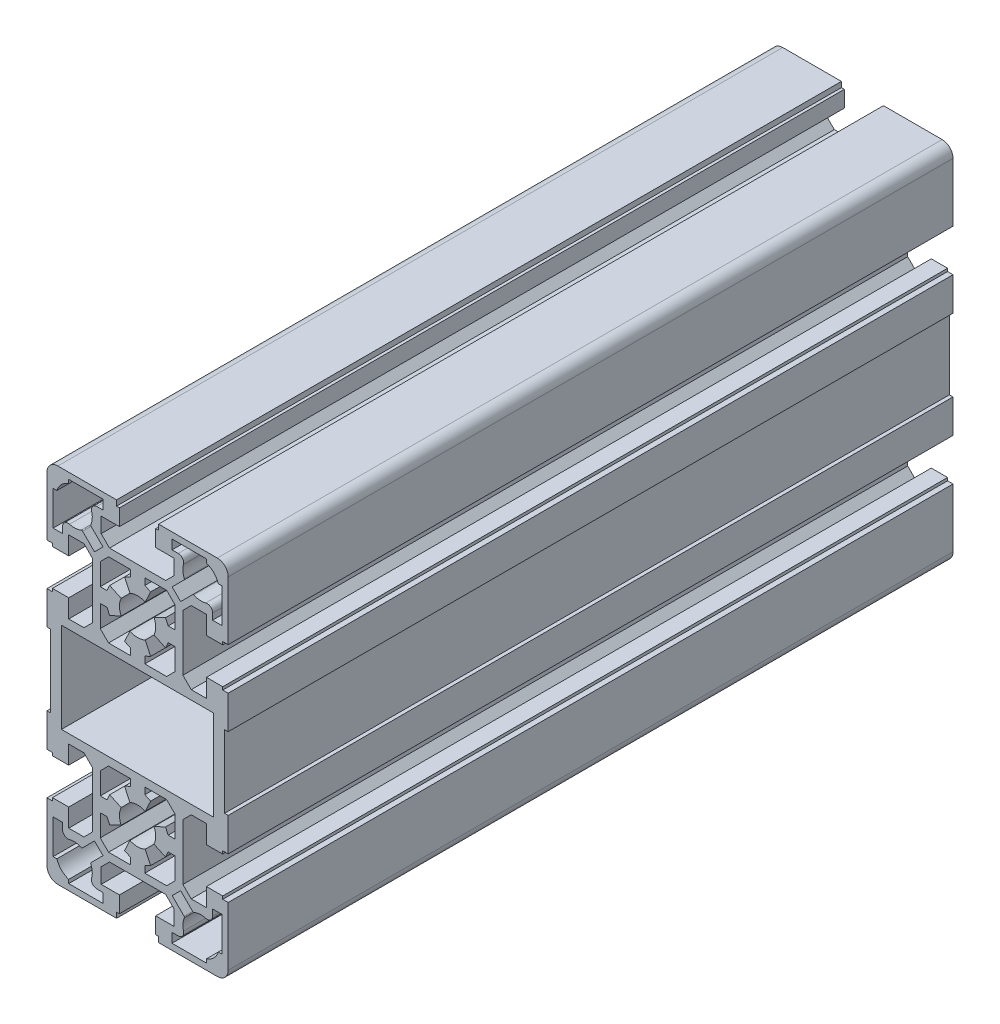
SolidWorks part; units mm, degrees
ref_plane "Front Plane" through (0, 0, 0) normal (0, 0, 1) x (1, 0, 0)
ref_plane "Top Plane" through (0, 0, 0) normal (0, 1, 0) x (1, 0, 0)
ref_plane "Right Plane" through (0, 0, 0) normal (1, 0, 0) x (0, 0, -1)
sketch "Sketch1" plane through (0, 0, 0) normal (0, 0, 1) x (1, 0, 0)
  line L0 (9.5389, 61.8847) -> (12.8447, 65.1906)
  line L1 (25, 72) -> (25, 55.8)
  line L2 (23.3, 69) -> (23.3, 59.5)
  line L3 (-10.05, 64.8) -> (-7.75, 62.5)
  line L4 (-12.8447, 65.1906) -> (-9.5389, 61.8847)
  line L5 (-25, 55.8) -> (-25, 72)
  line L6 (-23.3, 59.5) -> (-23.3, 69)
  line L7 (7.75, 62.5) -> (10.05, 64.8)
  line L8 (2, 60.3) -> (8.0123, 60.3)
  line L9 (-7.75, 62.5) -> (7.75, 62.5)
  line L10 (4.5315, 47.8869) -> (7.7036, 46.4077)
  line L11 (8.0123, 39.7) -> (2, 39.7)
  line L12 (7.7036, 53.5923) -> (4.5315, 52.1131)
  line L13 (8.0123, -10.3) -> (2, -10.3)
  line L14 (2, 10.3) -> (8.0123, 10.3)
  line L15 (7.7036, 3.5923) -> (4.5315, 2.1131)
  line L16 (4.5315, -2.1131) -> (7.7036, -3.5923)
  line L17 (7.75, -12.5) -> (-7.75, -12.5)
  line L18 (5, -19) -> (10.05, -19)
  line L19 (22, -25) -> (5.8, -25)
  line L20 (-21, 37.45) -> (21, 37.45)
  line L21 (21, 12.55) -> (-21, 12.55)
  line L22 (-24, 15) -> (-24, 35)
  line L23 (-21, 12.55) -> (-21, 37.45)
  line L24 (3.5923, -7.7036) -> (2.1131, -4.5315)
  line L25 (-2.1131, -4.5315) -> (-3.5923, -7.7036)
  line L26 (-10.3, -8.0123) -> (-10.3, -2)
  line L27 (-12.5, -7.75) -> (-12.5, 7.75)
  line L28 (-19, -5) -> (-19, -10.05)
  line L29 (-25, -22) -> (-25, -5.8)
  line L30 (-10.05, -14.8) -> (-10.05, -19)
  line L31 (-23.3, -19) -> (-23.3, -9.5)
  line L32 (-5.8, -25) -> (-22, -25)
  line L33 (-9.5, -23.3) -> (-19, -23.3)
  line L34 (-22.2697, -19) -> (-23.3, -19)
  line L35 (-19, -23.3) -> (-19, -22.2697)
  line L36 (5.8, -25) -> (5.8, -23.5)
  line L37 (-5.8, -23.5) -> (-5.8, -25)
  line L38 (-10.05, -19) -> (-5, -19)
  line L39 (-11.2262, -20.7) -> (-9.5, -20.7)
  line L40 (-5, -23.5) -> (-5.8, -23.5)
  line L41 (-5, -19) -> (-5, -23.5)
  line L42 (-9.5, -20.7) -> (-9.5, -23.3)
  line L43 (5.8, -23.5) -> (5, -23.5)
  line L44 (5, -23.5) -> (5, -19)
  line L45 (-14.8, -10.05) -> (-12.5, -7.75)
  line L46 (-15.1906, -12.8447) -> (-11.8847, -9.5389)
  line L47 (-19, -10.05) -> (-14.8, -10.05)
  line L48 (-20.7, -9.5) -> (-20.7, -11.2262)
  line L49 (-23.3, -9.5) -> (-20.7, -9.5)
  line L50 (-9.5389, -11.8847) -> (-12.8447, -15.1906)
  line L51 (-7.75, -12.5) -> (-10.05, -14.8)
  line L52 (-3.5923, -7.7036) -> (-2, -8.4461)
  line L53 (-2, -10.3) -> (-8.0123, -10.3)
  line L54 (-11.8847, -9.5389) -> (-9.5389, -11.8847)
  line L55 (-8.0123, -10.3) -> (-10.3, -8.0123)
  line L56 (2, -10.3) -> (2, -8.4461)
  line L57 (2, -8.4461) -> (3.5923, -7.7036)
  line L58 (-2, -8.4461) -> (-2, -10.3)
  line L59 (2.1131, 4.5315) -> (3.5923, 7.7036)
  line L60 (-10.3, 2) -> (-10.3, 8.0123)
  line L61 (-3.5923, 7.7036) -> (-2.1131, 4.5315)
  line L62 (-19, 10.05) -> (-19, 5)
  line L63 (-23.5, 5) -> (-23.5, 5.8)
  line L64 (-25, -5.8) -> (-23.5, -5.8)
  line L65 (-23.5, -5.8) -> (-23.5, -5)
  line L66 (-23.5, -5) -> (-19, -5)
  line L67 (-19, 5) -> (-23.5, 5)
  line L68 (-10.3, -2) -> (-8.4461, -2)
  line L69 (-8.4461, -2) -> (-7.7036, -3.5923)
  line L70 (-7.7036, -3.5923) -> (-4.5315, -2.1131)
  line L71 (-4.5315, 2.1131) -> (-7.7036, 3.5923)
  line L72 (-7.7036, 3.5923) -> (-8.4461, 2)
  line L73 (-8.4461, 2) -> (-10.3, 2)
  line L74 (-12.5, 7.75) -> (-14.8, 10.05)
  line L75 (-25, 5.8) -> (-25, 15)
  line L76 (-23.5, 5.8) -> (-25, 5.8)
  line L77 (-14.8, 10.05) -> (-19, 10.05)
  line L78 (-25, 15) -> (-24, 15)
  line L79 (-8.0123, 10.3) -> (-2, 10.3)
  line L80 (-2, 8.4461) -> (-3.5923, 7.7036)
  line L81 (-10.3, 8.0123) -> (-8.0123, 10.3)
  line L82 (3.5923, 7.7036) -> (2, 8.4461)
  line L83 (2, 8.4461) -> (2, 10.3)
  line L84 (-2, 10.3) -> (-2, 8.4461)
  line L85 (2, 39.7) -> (2, 41.5539)
  line L86 (-2, 41.5539) -> (-2, 39.7)
  line L87 (-8.0123, 39.7) -> (-10.3, 41.9877)
  line L88 (-25, 35) -> (-25, 44.2)
  line L89 (-24, 35) -> (-25, 35)
  line L90 (-2, 39.7) -> (-8.0123, 39.7)
  line L91 (-12.5, 42.25) -> (-12.5, 57.75)
  line L92 (-14.8, 39.95) -> (-12.5, 42.25)
  line L93 (-25, 44.2) -> (-23.5, 44.2)
  line L94 (-19, 39.95) -> (-14.8, 39.95)
  line L95 (-19, 45) -> (-19, 39.95)
  line L96 (-23.5, 44.2) -> (-23.5, 45)
  line L97 (-23.5, 45) -> (-19, 45)
  line L98 (-10.3, 41.9877) -> (-10.3, 48)
  line L99 (-2.1131, 45.4685) -> (-3.5923, 42.2964)
  line L100 (-3.5923, 42.2964) -> (-2, 41.5539)
  line L101 (2, 41.5539) -> (3.5923, 42.2964)
  line L102 (3.5923, 42.2964) -> (2.1131, 45.4685)
  line L103 (-10.3, 48) -> (-8.4461, 48)
  line L104 (-8.4461, 48) -> (-7.7036, 46.4077)
  line L105 (-7.7036, 46.4077) -> (-4.5315, 47.8869)
  line L106 (-12.5, 57.75) -> (-14.8, 60.05)
  line L107 (-11.8847, 59.5389) -> (-15.1906, 62.8447)
  line L108 (-19, 60.05) -> (-19, 55)
  line L109 (-23.5, 55.8) -> (-25, 55.8)
  line L110 (-23.5, 55) -> (-23.5, 55.8)
  line L111 (-19, 55) -> (-23.5, 55)
  line L112 (-14.8, 60.05) -> (-19, 60.05)
  line L113 (-20.7, 59.5) -> (-23.3, 59.5)
  line L114 (-20.7, 61.2262) -> (-20.7, 59.5)
  line L115 (2.1131, 54.5315) -> (3.5923, 57.7036)
  line L116 (-10.3, 52) -> (-10.3, 58.0123)
  line L117 (-3.5923, 57.7036) -> (-2.1131, 54.5315)
  line L118 (-4.5315, 52.1131) -> (-7.7036, 53.5923)
  line L119 (-7.7036, 53.5923) -> (-8.4461, 52)
  line L120 (-8.4461, 52) -> (-10.3, 52)
  line L121 (-8.0123, 60.3) -> (-2, 60.3)
  line L122 (-2, 58.4461) -> (-3.5923, 57.7036)
  line L123 (-10.3, 58.0123) -> (-8.0123, 60.3)
  line L124 (-9.5389, 61.8847) -> (-11.8847, 59.5389)
  line L125 (3.5923, 57.7036) -> (2, 58.4461)
  line L126 (-2, 60.3) -> (-2, 58.4461)
  line L127 (2, 58.4461) -> (2, 60.3)
  line L128 (24, 35) -> (24, 15)
  line L129 (21, 37.45) -> (21, 12.55)
  line L130 (19, -10.05) -> (19, -5)
  line L131 (12.5, 7.75) -> (12.5, -7.75)
  line L132 (10.3, -2) -> (10.3, -8.0123)
  line L133 (25, -5.8) -> (25, -22)
  line L134 (23.3, -9.5) -> (23.3, -19)
  line L135 (10.05, -19) -> (10.05, -14.8)
  line L136 (19, -23.3) -> (9.5, -23.3)
  line L137 (9.5, -20.7) -> (11.2262, -20.7)
  line L138 (9.5, -23.3) -> (9.5, -20.7)
  line L139 (23.3, -19) -> (22.2697, -19)
  line L140 (19, -22.2697) -> (19, -23.3)
  line L141 (12.8447, -15.1906) -> (9.5389, -11.8847)
  line L142 (11.8847, -9.5389) -> (15.1906, -12.8447)
  line L143 (10.05, -14.8) -> (7.75, -12.5)
  line L144 (14.8, -10.05) -> (19, -10.05)
  line L145 (12.5, -7.75) -> (14.8, -10.05)
  line L146 (9.5389, -11.8847) -> (11.8847, -9.5389)
  line L147 (10.3, -8.0123) -> (8.0123, -10.3)
  line L148 (20.7, -11.2262) -> (20.7, -9.5)
  line L149 (20.7, -9.5) -> (23.3, -9.5)
  line L150 (23.5, 5.8) -> (23.5, 5)
  line L151 (19, 5) -> (19, 10.05)
  line L152 (10.3, 8.0123) -> (10.3, 2)
  line L153 (7.7036, -3.5923) -> (8.4461, -2)
  line L154 (8.4461, -2) -> (10.3, -2)
  line L155 (23.5, -5.8) -> (25, -5.8)
  line L156 (23.5, -5) -> (23.5, -5.8)
  line L157 (19, -5) -> (23.5, -5)
  line L158 (8.4461, 2) -> (7.7036, 3.5923)
  line L159 (10.3, 2) -> (8.4461, 2)
  line L160 (23.5, 5) -> (19, 5)
  line L161 (25, 15) -> (25, 5.8)
  line L162 (19, 10.05) -> (14.8, 10.05)
  line L163 (14.8, 10.05) -> (12.5, 7.75)
  line L164 (8.0123, 10.3) -> (10.3, 8.0123)
  line L165 (25, 5.8) -> (23.5, 5.8)
  line L166 (24, 15) -> (25, 15)
  line L167 (25, 44.2) -> (25, 35)
  line L168 (10.3, 41.9877) -> (8.0123, 39.7)
  line L169 (25, 35) -> (24, 35)
  line L170 (12.5, 57.75) -> (12.5, 42.25)
  line L171 (10.3, 48) -> (10.3, 41.9877)
  line L172 (14.8, 39.95) -> (19, 39.95)
  line L173 (12.5, 42.25) -> (14.8, 39.95)
  line L174 (23.5, 44.2) -> (25, 44.2)
  line L175 (23.5, 45) -> (23.5, 44.2)
  line L176 (19, 39.95) -> (19, 45)
  line L177 (19, 45) -> (23.5, 45)
  line L178 (7.7036, 46.4077) -> (8.4461, 48)
  line L179 (8.4461, 48) -> (10.3, 48)
  line L180 (10.3, 58.0123) -> (10.3, 52)
  line L181 (19, 55) -> (19, 60.05)
  line L182 (8.4461, 52) -> (7.7036, 53.5923)
  line L183 (10.3, 52) -> (8.4461, 52)
  line L184 (23.5, 55.8) -> (23.5, 55)
  line L185 (25, 55.8) -> (23.5, 55.8)
  line L186 (23.5, 55) -> (19, 55)
  line L187 (19, 60.05) -> (14.8, 60.05)
  line L188 (14.8, 60.05) -> (12.5, 57.75)
  line L189 (15.1906, 62.8447) -> (11.8847, 59.5389)
  line L190 (11.8847, 59.5389) -> (9.5389, 61.8847)
  line L191 (8.0123, 60.3) -> (10.3, 58.0123)
  line L192 (23.3, 59.5) -> (20.7, 59.5)
  line L193 (20.7, 59.5) -> (20.7, 61.2262)
  line L194 (5.8, 75) -> (22, 75)
  line L195 (10.05, 69) -> (5, 69)
  line L196 (5.8, 73.5) -> (5.8, 75)
  line L197 (-5.8, 75) -> (-5.8, 73.5)
  line L198 (-19, 73.3) -> (-9.5, 73.3)
  line L199 (-19, 72.2697) -> (-19, 73.3)
  line L200 (-23.3, 69) -> (-22.2697, 69)
  line L201 (-10.05, 69) -> (-10.05, 64.8)
  line L202 (-5, 69) -> (-10.05, 69)
  line L203 (-5, 73.5) -> (-5, 69)
  line L204 (-5.8, 73.5) -> (-5, 73.5)
  line L205 (-9.5, 73.3) -> (-9.5, 70.7)
  line L206 (-9.5, 70.7) -> (-11.2262, 70.7)
  line L207 (5, 73.5) -> (5.8, 73.5)
  line L208 (5, 69) -> (5, 73.5)
  line L209 (-22, 75) -> (-5.8, 75)
  line L210 (10.05, 64.8) -> (10.05, 69)
  line L211 (9.5, 73.3) -> (19, 73.3)
  line L212 (11.2262, 70.7) -> (9.5, 70.7)
  line L213 (9.5, 70.7) -> (9.5, 73.3)
  line L214 (22.2697, 69) -> (23.3, 69)
  line L215 (19, 73.3) -> (19, 72.2697)
  line L216 (-31.2795, 25) -> (51.8378, 25) construction
  line L217 (0, 92.7584) -> (0, -39.4357) construction
  arc A0 (20.7, 61.2262) -> (18.8077, 62.674) centre (19.2, 61.2262) ccw
  arc A1 (-18.8077, 62.674) -> (-20.7, 61.2262) centre (-19.2, 61.2262) ccw
  arc A2 (-12.674, -18.8077) -> (-12.9081, -15.5214) centre (-17.5, -17.5) ccw
  arc A3 (-25, -22) -> (-22, -25) centre (-22, -22) ccw
  arc A4 (-22.2697, -19) -> (-19, -22.2697) centre (-17.5, -17.5) ccw
  arc A5 (-12.674, -18.8077) -> (-11.2262, -20.7) centre (-11.2262, -19.2) ccw
  arc A6 (-20.7, -11.2262) -> (-18.8077, -12.674) centre (-19.2, -11.2262) ccw
  arc A7 (-15.5214, -12.9081) -> (-18.8077, -12.674) centre (-17.5, -17.5) ccw
  arc A8 (-15.5214, -12.9081) -> (-15.1906, -12.8447) centre (-15.4027, -12.6326) ccw
  arc A9 (-12.8447, -15.1906) -> (-12.9081, -15.5214) centre (-12.6326, -15.4027) ccw
  arc A10 (4.5315, -2.1131) -> (4.5315, 2.1131) centre (0, 0) ccw
  arc A11 (-4.5315, 2.1131) -> (-4.5315, -2.1131) centre (0, 0) ccw
  arc A12 (-2.1131, -4.5315) -> (2.1131, -4.5315) centre (0, 0) ccw
  arc A13 (2.1131, 4.5315) -> (-2.1131, 4.5315) centre (0, 0) ccw
  arc A14 (4.5315, 47.8869) -> (4.5315, 52.1131) centre (0, 50) ccw
  arc A15 (-4.5315, 52.1131) -> (-4.5315, 47.8869) centre (0, 50) ccw
  arc A16 (-2.1131, 45.4685) -> (2.1131, 45.4685) centre (0, 50) ccw
  arc A17 (-15.1906, 62.8447) -> (-15.5214, 62.9081) centre (-15.4027, 62.6326) ccw
  arc A18 (-18.8077, 62.674) -> (-15.5214, 62.9081) centre (-17.5, 67.5) ccw
  arc A19 (2.1131, 54.5315) -> (-2.1131, 54.5315) centre (0, 50) ccw
  arc A20 (12.9081, -15.5214) -> (12.674, -18.8077) centre (17.5, -17.5) ccw
  arc A21 (22, -25) -> (25, -22) centre (22, -22) ccw
  arc A22 (11.2262, -20.7) -> (12.674, -18.8077) centre (11.2262, -19.2) ccw
  arc A23 (19, -22.2697) -> (22.2697, -19) centre (17.5, -17.5) ccw
  arc A24 (18.8077, -12.674) -> (20.7, -11.2262) centre (19.2, -11.2262) ccw
  arc A25 (18.8077, -12.674) -> (15.5214, -12.9081) centre (17.5, -17.5) ccw
  arc A26 (12.9081, -15.5214) -> (12.8447, -15.1906) centre (12.6326, -15.4027) ccw
  arc A27 (15.1906, -12.8447) -> (15.5214, -12.9081) centre (15.4027, -12.6326) ccw
  arc A28 (15.5214, 62.9081) -> (18.8077, 62.674) centre (17.5, 67.5) ccw
  arc A29 (15.5214, 62.9081) -> (15.1906, 62.8447) centre (15.4027, 62.6326) ccw
  arc A30 (-22, 75) -> (-25, 72) centre (-22, 72) ccw
  arc A31 (-19, 72.2697) -> (-22.2697, 69) centre (-17.5, 67.5) ccw
  arc A32 (-11.2262, 70.7) -> (-12.674, 68.8077) centre (-11.2262, 69.2) ccw
  arc A33 (-12.9081, 65.5214) -> (-12.674, 68.8077) centre (-17.5, 67.5) ccw
  arc A34 (-12.9081, 65.5214) -> (-12.8447, 65.1906) centre (-12.6326, 65.4027) ccw
  arc A35 (25, 72) -> (22, 75) centre (22, 72) ccw
  arc A36 (12.674, 68.8077) -> (11.2262, 70.7) centre (11.2262, 69.2) ccw
  arc A37 (12.8447, 65.1906) -> (12.9081, 65.5214) centre (12.6326, 65.4027) ccw
  arc A38 (12.674, 68.8077) -> (12.9081, 65.5214) centre (17.5, 67.5) ccw
  arc A39 (22.2697, 69) -> (19, 72.2697) centre (17.5, 67.5) ccw
  dimension "D4" = 10
  dimension "D5" = 10
  dimension "D1" = 100
  dimension "D2" = 50
  dimension "D3" = 10
  dimension "D6" = 10
extrude "Base-Extrude" add sketch "Sketch1" along normal blind 200
